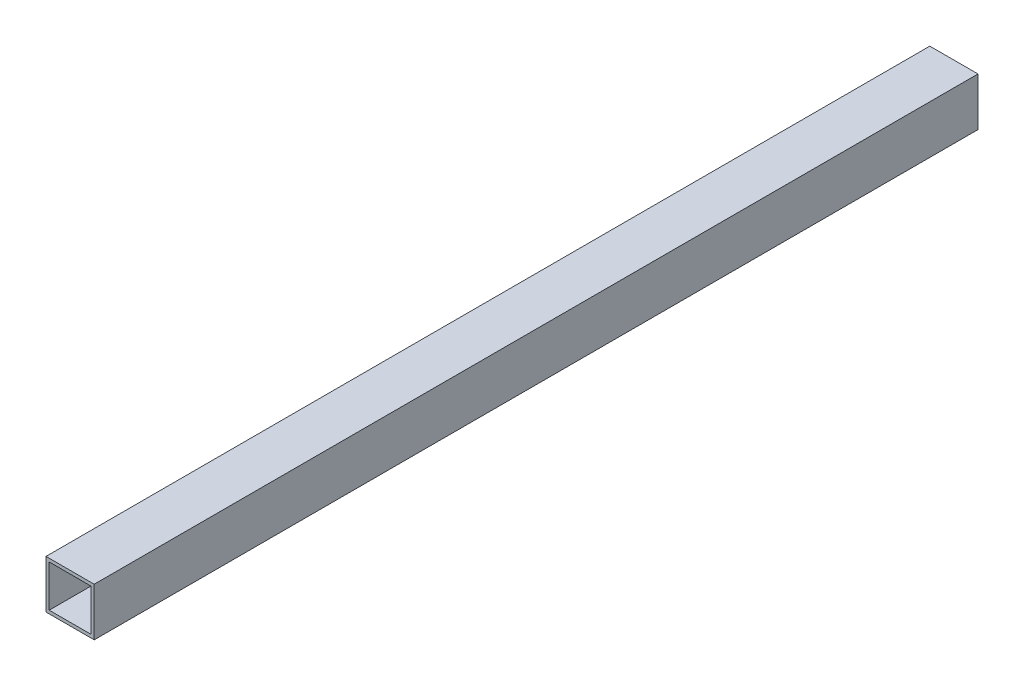
SolidWorks part; units mm, degrees
ref_plane "Front Plane" through (0, 0, 0) normal (0, 0, 1) x (1, 0, 0)
ref_plane "Top Plane" through (0, 0, 0) normal (0, 1, 0) x (1, 0, 0)
ref_plane "Right Plane" through (0, 0, 0) normal (1, 0, 0) x (0, 0, -1)
sketch "Esboço2" plane through (0, 0, 0) normal (0, 0, 1) x (1, 0, 0)
  line L1 (-94.2052, 59.6622) -> (-64.2052, 59.6622)
  line L2 (-94.2052, 59.6622) -> (-94.2052, 29.6622)
  line L3 (-94.2052, 29.6622) -> (-64.2052, 29.6622)
  line L4 (-64.2052, 59.6622) -> (-64.2052, 29.6622)
  dimension "D1" = 30
  dimension "D2" = 30
extrude "Ressalto-extrusão1" add sketch "Esboço2" along normal blind 550
shell "Casca2" thickness 2
